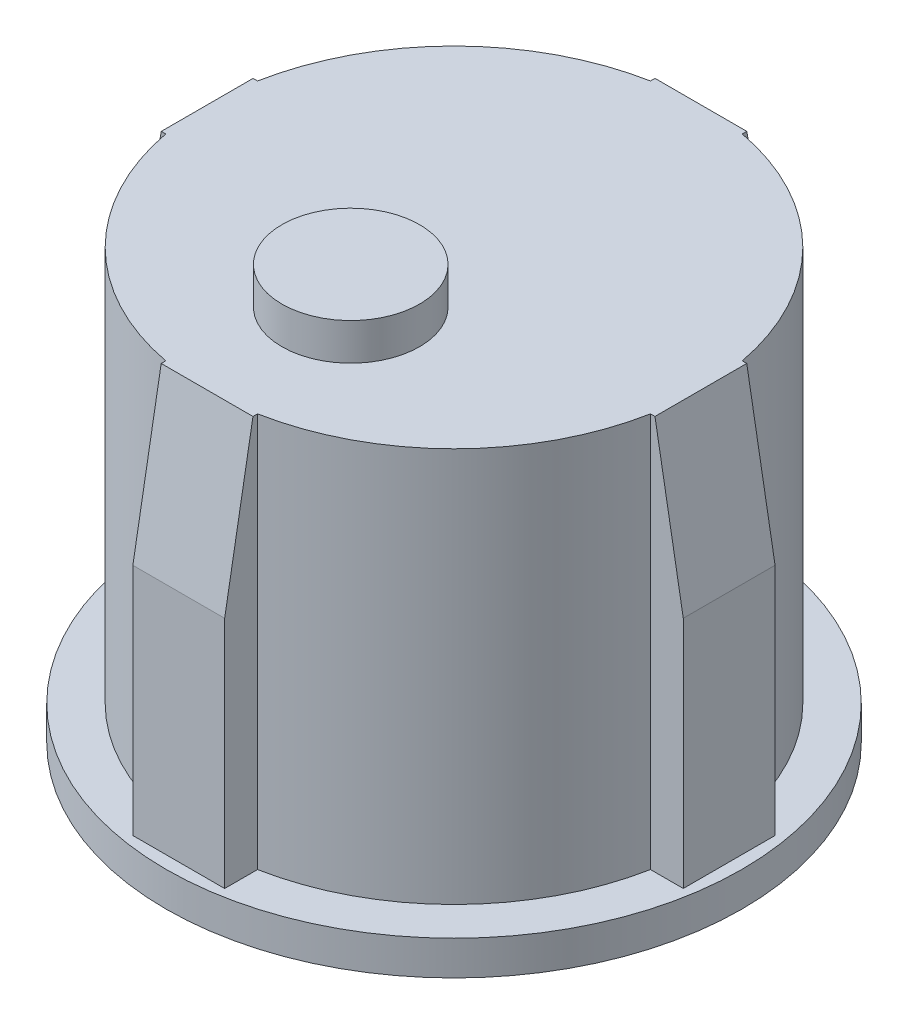
SolidWorks part; units mm, degrees
ref_plane "Front Plane" through (0, 0, 0) normal (0, 0, 1) x (1, 0, 0)
ref_plane "Top Plane" through (0, 0, 0) normal (0, 1, 0) x (1, 0, 0)
ref_plane "Right Plane" through (0, 0, 0) normal (1, 0, 0) x (0, 0, -1)
sketch "Sketch1" plane through (0, 0, 0) normal (0, 1, 0) x (1, 0, 0)
  circle A0 centre (0, 0) radius 12.55
  dimension "D1" = 25.1
extrude "Boss-Extrude1" add sketch "Sketch1" along normal blind 1.5
sketch "Sketch2" plane through (0, 1.5, 0) normal (0, 1, 0) x (1, 0, 0)
  circle A0 centre (0, 0) radius 10.75
  dimension "D1" = 21.5
extrude "Boss-Extrude2" add sketch "Sketch2" along normal blind 17.2 contours A0
sketch "Sketch3" plane through (0, 1.5, 0) normal (0, 1, 0) x (1, 0, 0)
  line L0 (-12.55, 0) -> (12.55, 0) construction
  line L1 (0, 12.55) -> (0, -12.55) construction
  line L2 (2, 11.9949) -> (-2, 11.9949)
  line L3 (-2, 11.9949) -> (-2, 10.5623)
  line L4 (-11.9923, -2) -> (-11.9923, 2)
  line L5 (-11.9923, 2) -> (-10.5623, 2)
  line L6 (2, 11.9949) -> (2, 10.5623)
  line L7 (-2, -11.9949) -> (-2, -10.5623)
  line L8 (2, -11.9949) -> (-2, -11.9949)
  line L9 (2, -11.9949) -> (2, -10.5623)
  line L10 (-11.9923, -2) -> (-10.5623, -2)
  line L11 (11.9923, -2) -> (10.5623, -2)
  line L12 (11.9923, -2) -> (11.9923, 2)
  line L13 (11.9923, 2) -> (10.5623, 2)
  circle A0 centre (0, 0) radius 10.75 construction
  arc A1 (-10.5623, 2) -> (-10.5623, -2) centre (0, 0) ccw
  circle A2 centre (0, 0) radius 12.55 construction
  arc A3 (-2, -10.5623) -> (2, -10.5623) centre (0, 0) ccw
  arc A4 (2, 10.5623) -> (-2, 10.5623) centre (0, 0) ccw
  arc A5 (10.5623, -2) -> (10.5623, 2) centre (0, 0) ccw
  point P17 (0, 11.9949)
  point P24 (-11.9923, 0)
  dimension "D1" = 2
  dimension "D2" = 1.4326
  dimension "D3" = 2
  dimension "D4" = 1.43
extrude "Boss-Extrude3" add sketch "Sketch3" along normal blind 17.2
sketch "Sketch4" plane through (0, 18.7, 0) normal (0, 1, 0) x (1, 0, 0)
  circle A0 centre (0, -4.5) radius 3
  dimension "D1" = 6
  dimension "D2" = 4.5
extrude "Boss-Extrude4" add sketch "Sketch4" along normal blind 1.61
sketch "Sketch5" plane through (0, 0, 0) normal (0, -1, 0) x (1, 0, 0)
  circle A0 centre (0, 0) radius 6
  circle A1 centre (0, 0) radius 7
  dimension "D1" = 12
  dimension "D2" = 14
extrude "Cut-Extrude1" cut sketch "Sketch5" against normal blind 1
chamfer "Chamfer1" distance 7 angle 10 4 edges at (0, 18.7, -11.9949) (-11.9923, 18.7, 0) (11.9923, 18.7, 0) (0, 18.7, 11.9949)
equation "\"0.5.00mm\"=10"
